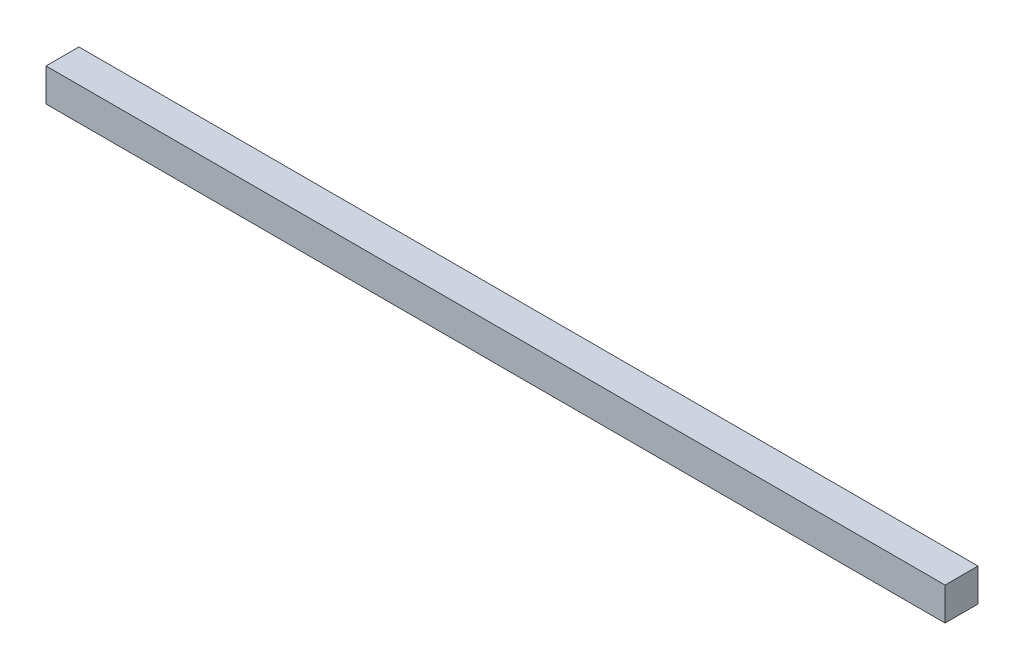
SolidWorks part; units mm, degrees
ref_plane "Plan de face" through (0, 0, 0) normal (0, 0, 1) x (1, 0, 0)
ref_plane "Plan de dessus" through (0, 0, 0) normal (0, 1, 0) x (1, 0, 0)
ref_plane "Plan de droite" through (0, 0, 0) normal (1, 0, 0) x (0, 0, -1)
sketch "Esquisse1" plane through (0, 0, 0) normal (0, 0, 1) x (1, 0, 0)
  line L1 (-217.8166, 74.7917) -> (55.1834, 74.7917)
  line L2 (-217.8166, 74.7917) -> (-217.8166, 64.7917)
  line L3 (-217.8166, 64.7917) -> (55.1834, 64.7917)
  line L4 (55.1834, 74.7917) -> (55.1834, 64.7917)
  dimension "D1" = 10
  dimension "D2" = 273
extrude "Boss.-Extru.1" add sketch "Esquisse1" along normal blind 10 contours L1 L4 L3 L2
equation "\"EpaisseurPlaque\"= 3"
equation "\"ProfondeurBoite\"=460"
equation "\"LongueurSyphon\"=270"
equation "\"LargeurSyphon\"=120"
equation "\"HauteurCoteDroit\"= 490"
equation "\"HauteurCoteGauche\"= 540"
equation "\"HauteurSolSyphon\"= 300"
equation "\"HauteurSyphon\"=\"HauteurCoteGauche\"-\"HauteurSolSyphon\""
equation "\"LargeurDroite\"=10"
equation "\"LargeurGauche\"=150"
equation "\"LargeurBoite\"= \"LargeurDroite\" + \"LargeurGauche\" + \"LargeurSyphon\""
equation "\"D2@Esquisse1\"=\"LongueurSyphon\" +3"
